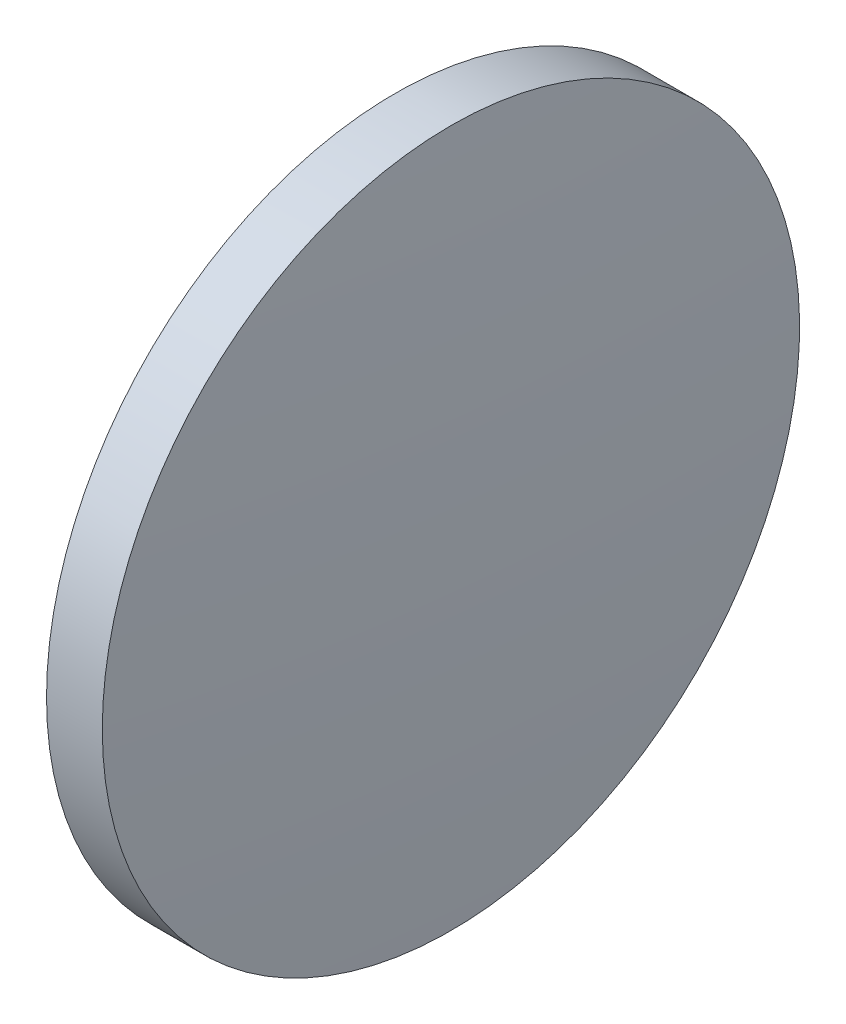
SolidWorks part; units mm, degrees
ref_plane "前视基准面" through (0, 0, 0) normal (0, 0, 1) x (1, 0, 0)
ref_plane "上视基准面" through (0, 0, 0) normal (0, 1, 0) x (1, 0, 0)
ref_plane "右视基准面" through (0, 0, 0) normal (1, 0, 0) x (0, 0, -1)
sketch "草图1" plane through (0, 0, 0) normal (0, 0, 1) x (1, 0, 0)
  line L0 (376.9291, 209.0414) -> (386.5171, 209.0414) construction
  line L1 (379.2947, 209.0414) -> (379.2947, 221.5414)
  line L2 (381.6747, 209.0414) -> (379.2947, 209.0414)
  line L5 (379.2947, 221.5414) -> (381.2947, 221.5414)
  arc A0 (381.6747, 209.0414) -> (381.2947, 221.5414) centre (175.8926, 209.0414) ccw
revolve "旋转1" add sketch "草图1" angle 360 about L0
